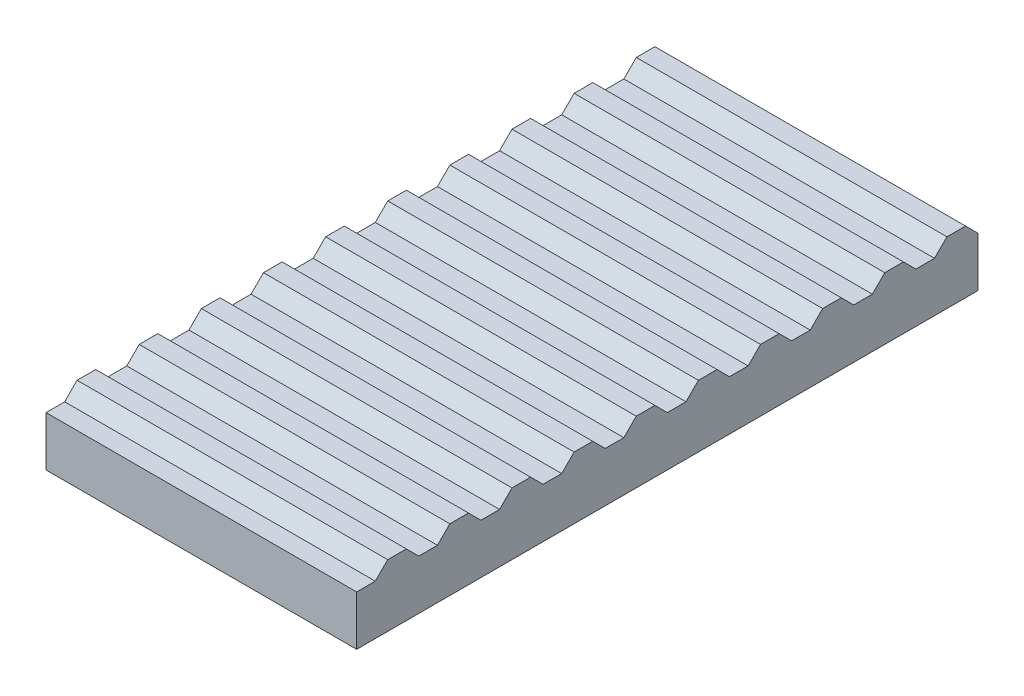
SolidWorks part; units mm, degrees
ref_plane "前视基准面" through (0, 0, 0) normal (0, 0, 1) x (1, 0, 0)
ref_plane "上视基准面" through (0, 0, 0) normal (0, 1, 0) x (1, 0, 0)
ref_plane "右视基准面" through (0, 0, 0) normal (1, 0, 0) x (0, 0, -1)
sketch "草图2" plane through (0, 0, 0) normal (1, 0, 0) x (0, 0, -1)
  line L0 (-10, 0) -> (10, 0)
  line L1 (10, 0) -> (10, 1.6)
  line L2 (10, 1.6) -> (9.6, 2)
  line L3 (9.6, 2) -> (9, 2)
  line L4 (9, 2) -> (8.6, 1.6)
  line L5 (8.6, 1.6) -> (8, 1.6)
  line L6 (6.6, 1.6) -> (6, 1.6)
  line L7 (7, 2) -> (6.6, 1.6)
  line L8 (7.6, 2) -> (7, 2)
  line L9 (8, 1.6) -> (7.6, 2)
  line L10 (0, 0) -> (0, -50000) construction
  line L11 (4.6, 1.6) -> (4, 1.6)
  line L12 (5, 2) -> (4.6, 1.6)
  line L13 (5.6, 2) -> (5, 2)
  line L14 (6, 1.6) -> (5.6, 2)
  line L15 (2.6, 1.6) -> (2, 1.6)
  line L16 (3, 2) -> (2.6, 1.6)
  line L17 (3.6, 2) -> (3, 2)
  line L18 (4, 1.6) -> (3.6, 2)
  line L19 (0.6, 1.6) -> (0, 1.6)
  line L20 (1, 2) -> (0.6, 1.6)
  line L21 (1.6, 2) -> (1, 2)
  line L22 (2, 1.6) -> (1.6, 2)
  line L23 (-1.4, 1.6) -> (-2, 1.6)
  line L24 (-1, 2) -> (-1.4, 1.6)
  line L25 (-0.4, 2) -> (-1, 2)
  line L26 (0, 1.6) -> (-0.4, 2)
  line L27 (-3.4, 1.6) -> (-4, 1.6)
  line L28 (-3, 2) -> (-3.4, 1.6)
  line L29 (-2.4, 2) -> (-3, 2)
  line L30 (-2, 1.6) -> (-2.4, 2)
  line L31 (-5.4, 1.6) -> (-6, 1.6)
  line L32 (-5, 2) -> (-5.4, 1.6)
  line L33 (-4.4, 2) -> (-5, 2)
  line L34 (-4, 1.6) -> (-4.4, 2)
  line L35 (-7.4, 1.6) -> (-8, 1.6)
  line L36 (-7, 2) -> (-7.4, 1.6)
  line L37 (-6.4, 2) -> (-7, 2)
  line L38 (-6, 1.6) -> (-6.4, 2)
  line L39 (-9.4, 1.6) -> (-10, 1.6)
  line L40 (-9, 2) -> (-9.4, 1.6)
  line L41 (-8.4, 2) -> (-9, 2)
  line L42 (-8, 1.6) -> (-8.4, 2)
  line L43 (-10, 0) -> (-10, 1.6)
  point P4 (0, 0)
  dimension "D1" = 45
  dimension "D2" = 1.6
  dimension "D3" = 20
  dimension "D4" = 0.4
  dimension "D5" = 0.6
  dimension "D6" = 10
extrude "凸台-拉伸1" add sketch "草图2" along normal blind 10
